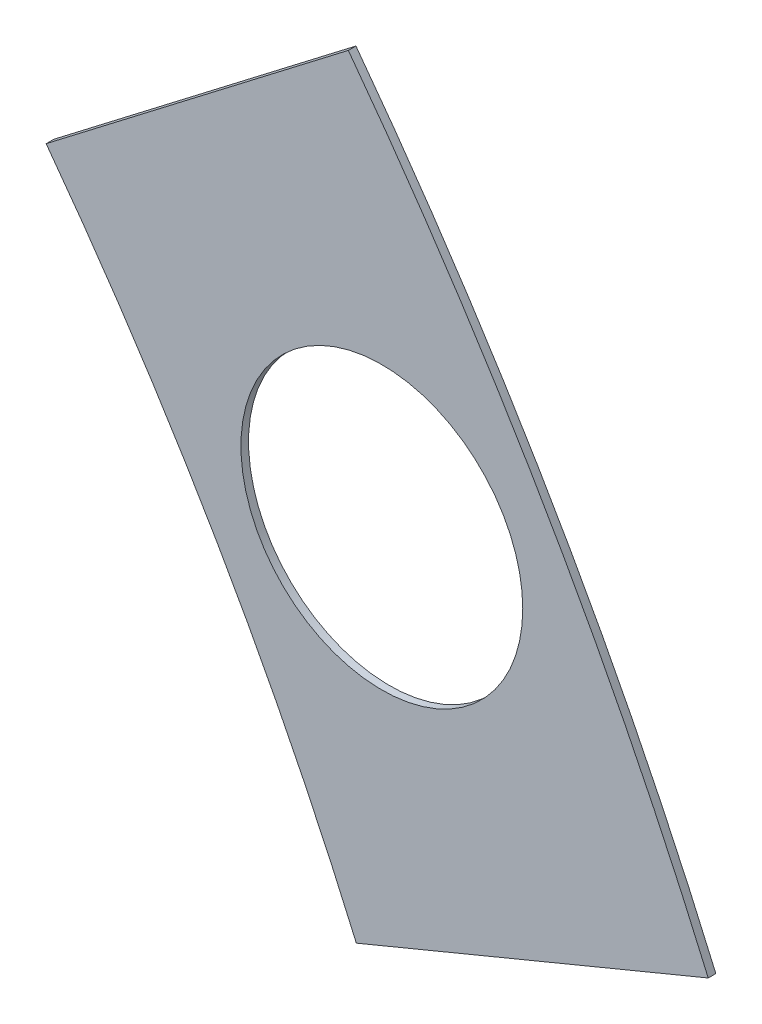
SolidWorks part; units mm, degrees
material "Copper"
ref_plane "Front Plane" through (0, 0, 0) normal (0, 0, 1) x (1, 0, 0)
ref_plane "Top Plane" through (0, 0, 0) normal (0, 1, 0) x (1, 0, 0)
ref_plane "Right Plane" through (0, 0, 0) normal (1, 0, 0) x (0, 0, -1)
sketch "Sketch1" plane through (0, 0, 0) normal (0, 0, 1) x (1, 0, 0)
  line L0 (0, 0) -> (320.3893, 0) construction
  line L1 (0, 0) -> (155.5285, 155.5285) construction
  line L2 (67.2115, 76.1917) -> (8.6967, 17.6769)
  line L3 (8.6967, 17.6769) -> (7.229, 14.1336)
  line L4 (101.4014, -6.35) -> (18.6489, -6.35)
  line L5 (15.1056, -4.8823) -> (18.6489, -6.35)
  line L6 (88.6729, 6.35) -> (27.8605, 6.35)
  line L9 (67.1914, 58.2111) -> (24.1905, 15.2102)
  line L10 (0, 0) -> (40.4486, 97.6516) construction
  line L11 (0, 0) -> (123.4567, -51.1374) construction
  line L18 (8.6967, 17.6769) -> (13.294, 8.6183) construction
  line L19 (18.6489, -6.35) -> (15.4943, 3.3063) construction
  line L20 (27.8605, 6.35) -> (27.7442, 6.7059) construction
  line L21 (24.1905, 15.2102) -> (24.3599, 14.8764) construction
  arc A0 (7.229, 14.1336) -> (15.1056, -4.8823) centre (0, 0) cw
  arc A1 (67.2115, 76.1917) -> (101.4014, -6.35) centre (0, 0) cw
  arc A2 (24.1905, 15.2102) -> (27.8605, 6.35) centre (0, 0) cw
  arc A3 (67.1914, 58.2111) -> (88.6729, 6.35) centre (0, 0) cw
  arc A8 (13.294, 8.6183) -> (15.4943, 3.3063) centre (0, 0) cw construction
  arc A9 (24.3599, 14.8764) -> (27.7442, 6.7059) centre (0, 0) cw construction
  dimension "D1" = 45
  dimension "D3" = 6.35
  dimension "D4" = 15.875
  dimension "D7" = 22.5
  dimension "D8" = 101.6
  dimension "D11" = 12.7
  dimension "D12" = 12.7
  dimension "D2" = 6.35
  dimension "D5" = 67.5
  dimension "D9" = 1.27
  dimension "D10" = 1.27
  dimension "D6" = 12.7
extrude "Boss-Extrude1" add sketch "Sketch1" along normal blind 0.254
sketch "Sketch2" plane through (0, 0, 0.254) normal (0, 0, 1) x (1, 0, 0)
  line L0 (0, 0) -> (101.6, 0) construction
  line L1 (0, 0) -> (71.842, 71.842) construction
  line L3 (0, 0) -> (22.225, 0) construction
  line L4 (0, 0) -> (15.7154, 15.7154) construction
  line L5 (0, 0) -> (95.25, 0) construction
  line L6 (0, 0) -> (92.0044, 24.6525) construction
  arc A0 (101.4014, -6.35) -> (67.2115, 76.1917) centre (0, 0) ccw construction
  circle A1 centre (22.225, 0) radius 4.699
  arc A2 (15.1056, -4.8823) -> (7.229, 14.1336) centre (0, 0) ccw construction
  circle A3 centre (36.195, 0) radius 4.699
  circle A4 centre (61.722, 0) radius 4.699
  circle A5 centre (75.692, 0) radius 4.699
  circle A6 centre (95.25, 0) radius 4.699
  circle A7 centre (15.7154, 15.7154) radius 4.699
  circle A8 centre (25.5937, 25.5937) radius 4.699
  circle A9 centre (43.644, 43.644) radius 4.699
  circle A10 centre (53.5223, 53.5223) radius 4.699
  circle A11 centre (92.0044, 24.6525) radius 4.699
  circle A12 centre (82.4889, 47.625) radius 4.699
  circle A13 centre (67.3519, 67.3519) radius 4.699
  dimension "D3" = 9.398
  dimension "D1" = 45
  dimension "D2" = 6.35
  dimension "D4" = 6.35
  dimension "D5" = 13.97
  dimension "D7" = 13.97
  dimension "D8" = 19.558
  dimension "D9" = 45
  dimension "D10" = 15
  dimension "D11" = 25.527
  dimension "D6" = 2
extrude "Cut-Extrude1" cut sketch "Sketch2" against normal through all
sketch "Sketch3" plane through (0, 0, 0.254) normal (0, 0, 1) x (1, 0, 0)
  line L0 (15.2664, 24.2467) -> (17.0625, 26.0427)
  line L1 (15.2664, 24.2467) -> (15.7154, 23.7977)
  line L2 (17.0625, 26.0427) -> (17.5115, 25.5937)
  line L3 (15.7154, 23.7977) -> (17.5115, 25.5937)
  line L4 (67.2115, 76.1917) -> (8.6967, 17.6769) construction
  line L5 (44.9911, 53.9713) -> (43.195, 52.1753)
  line L6 (44.9911, 53.9713) -> (45.4401, 53.5223)
  line L7 (43.195, 52.1753) -> (43.644, 51.7263)
  line L8 (45.4401, 53.5223) -> (43.644, 51.7263)
  line L9 (27.94, -6.35) -> (30.48, -6.35)
  line L10 (27.94, -6.35) -> (27.94, -5.715)
  line L11 (30.48, -6.35) -> (30.48, -5.715)
  line L12 (27.94, -5.715) -> (30.48, -5.715)
  line L13 (18.6489, -6.35) -> (101.4014, -6.35) construction
  line L14 (67.437, -6.35) -> (69.977, -6.35)
  line L15 (67.437, -6.35) -> (67.437, -5.715)
  line L16 (69.977, -6.35) -> (69.977, -5.715)
  line L17 (67.437, -5.715) -> (69.977, -5.715)
  line L18 (29.2307, 38.211) -> (31.0268, 40.007)
  line L19 (29.2307, 38.211) -> (29.6797, 37.762)
  line L20 (31.0268, 40.007) -> (31.4758, 39.558)
  line L21 (29.6797, 37.762) -> (31.4758, 39.558)
  line L22 (56.845, 65.8253) -> (55.049, 64.0292)
  line L23 (56.845, 65.8253) -> (57.294, 65.3763)
  line L24 (55.049, 64.0292) -> (55.498, 63.5802)
  line L25 (57.294, 65.3763) -> (55.498, 63.5802)
  line L26 (47.6885, -6.35) -> (50.2285, -6.35)
  line L27 (47.6885, -6.35) -> (47.6885, -5.715)
  line L28 (50.2285, -6.35) -> (50.2285, -5.715)
  line L29 (47.6885, -5.715) -> (50.2285, -5.715)
  line L30 (84.201, -6.35) -> (86.741, -6.35)
  line L31 (84.201, -6.35) -> (84.201, -5.715)
  line L32 (86.741, -6.35) -> (86.741, -5.715)
  line L33 (84.201, -5.715) -> (86.741, -5.715)
  line L34 (0, 0) -> (100.7308, 13.2615) construction
  line L35 (0, 0) -> (93.8662, 38.8806) construction
  line L36 (0, 0) -> (80.6047, 61.8502) construction
  line L37 (0, 0) -> (101.6, 0) construction
  line L38 (99.9355, 14.4377) -> (100.267, 11.9194)
  line L39 (99.9355, 14.4377) -> (101.1946, 14.6035)
  line L40 (100.267, 11.9194) -> (101.5261, 12.0852)
  line L41 (101.1946, 14.6035) -> (101.5261, 12.0852)
  line L42 (99.9355, 14.4377) -> (101.5261, 12.0852) construction
  line L43 (100.267, 11.9194) -> (101.1946, 14.6035) construction
  line L44 (93.7655, 37.4643) -> (94.9388, 37.9503)
  line L45 (93.7655, 37.4643) -> (92.7935, 39.811)
  line L46 (94.9388, 37.9503) -> (93.9668, 40.297)
  line L47 (92.7935, 39.811) -> (93.9668, 40.297)
  line L48 (93.7655, 37.4643) -> (93.9668, 40.297) construction
  line L49 (94.9388, 37.9503) -> (92.7935, 39.811) construction
  line L50 (79.3278, 62.4712) -> (80.874, 60.456)
  line L51 (79.3278, 62.4712) -> (80.3354, 63.2443)
  line L52 (80.874, 60.456) -> (81.8816, 61.2292)
  line L53 (80.3354, 63.2443) -> (81.8816, 61.2292)
  line L54 (79.3278, 62.4712) -> (81.8816, 61.2292) construction
  line L55 (80.874, 60.456) -> (80.3354, 63.2443) construction
  line L56 (13.5939, 7.0054) -> (14.5659, 4.6588)
  line L57 (13.5939, 7.0054) -> (14.7672, 7.4914)
  line L58 (14.5659, 4.6588) -> (15.7393, 5.1448)
  line L59 (14.7672, 7.4914) -> (15.7393, 5.1448)
  line L60 (13.5939, 7.0054) -> (15.7393, 5.1448) construction
  line L61 (14.5659, 4.6588) -> (14.7672, 7.4914) construction
  circle A0 centre (15.7154, 15.7154) radius 4.699 construction
  circle A1 centre (43.644, 43.644) radius 4.699 construction
  circle A2 centre (22.225, 0) radius 4.699 construction
  circle A3 centre (61.722, 0) radius 4.699 construction
  arc A4 (101.4014, -6.35) -> (67.2115, 76.1917) centre (0, 0) ccw construction
  arc A9 (15.1056, -4.8823) -> (7.229, 14.1336) centre (0, 0) ccw construction
  circle A10 centre (36.195, 0) radius 4.699 construction
  circle A11 centre (75.692, 0) radius 4.699 construction
  circle A12 centre (25.5937, 25.5937) radius 4.699 construction
  circle A13 centre (53.5223, 53.5223) radius 4.699 construction
  point P75 (14.6666, 6.0751)
  dimension "D2" = 5.715
  dimension "D3" = 2.54
  dimension "D6" = 5.715
  dimension "D8" = 0.635
  dimension "D9" = 5.715
  dimension "D12" = 5.715
  dimension "D4" = 7.5
  dimension "D5" = 22.5
  dimension "D7" = 37.5
  dimension "D10" = 90
  dimension "D11" = 1.27
  dimension "D14" = 0.635
  dimension "D15" = 90
  dimension "D18" = 0.635
  dimension "D19" = 90
  dimension "D22" = 0.635
  dimension "D20" = 1.27
  dimension "D17" = 0.635
  dimension "D13" = 11.4935
  dimension "D16" = 8.509
  dimension "D21" = 11.4935
  dimension "D23" = 8.509
extrude "Cut-Extrude2" cut sketch "Sketch3" against normal through all
sketch "Sketch5" plane through (0, 0, 0.254) normal (0, 0, 1) x (1, 0, 0)
  line L0 (0, 0) -> (85.7359, 65.7875) construction
  line L1 (0, 0) -> (99.6979, 41.2962) construction
  line L2 (69.977, -6.35) -> (84.201, -6.35) construction
  line L3 (93.7655, 37.4643) -> (94.3448, 37.7043) construction
  line L4 (70.2874, 52.3326) -> (82.3792, 61.611)
  line L5 (80.4651, 34.7044) -> (94.5462, 40.537)
  line L6 (79.8253, 62.8529) -> (79.3278, 62.4712) construction
  arc A0 (80.4651, 34.7044) -> (70.2874, 52.3326) centre (0, 0) ccw
  arc A1 (94.5462, 40.537) -> (82.3792, 61.611) centre (0, 0) ccw
  arc A2 (93.3728, 40.0509) -> (81.3715, 60.8378) centre (0, 0) ccw construction
  arc A3 (88.6729, 6.35) -> (67.1914, 58.2111) centre (0, 0) ccw construction
  dimension "D5" = 1.27
  dimension "D6" = 1.27
  dimension "D1" = 37.5
  dimension "D2" = 22.5
  dimension "D3" = 2.54
  dimension "D4" = 2.54
extrude "Cut-Extrude5" cut sketch "Sketch5" against normal through all flip side to cut
equation "\"cSep\"= 1.005"
equation "\"D11@Sketch2\"=\"cSep\""
equation "\"cSep2\"= \"D8@Sketch2\""
equation "\"D13@Sketch3\"=\"cSep\"/2-.05"
equation "\"D16@Sketch3\"=\"cSep2\"/2-.05"
equation "\"D21@Sketch3\"=\"cSep\"/2-.05"
equation "\"D23@Sketch3\"=\"cSep2\"/2-.05"
